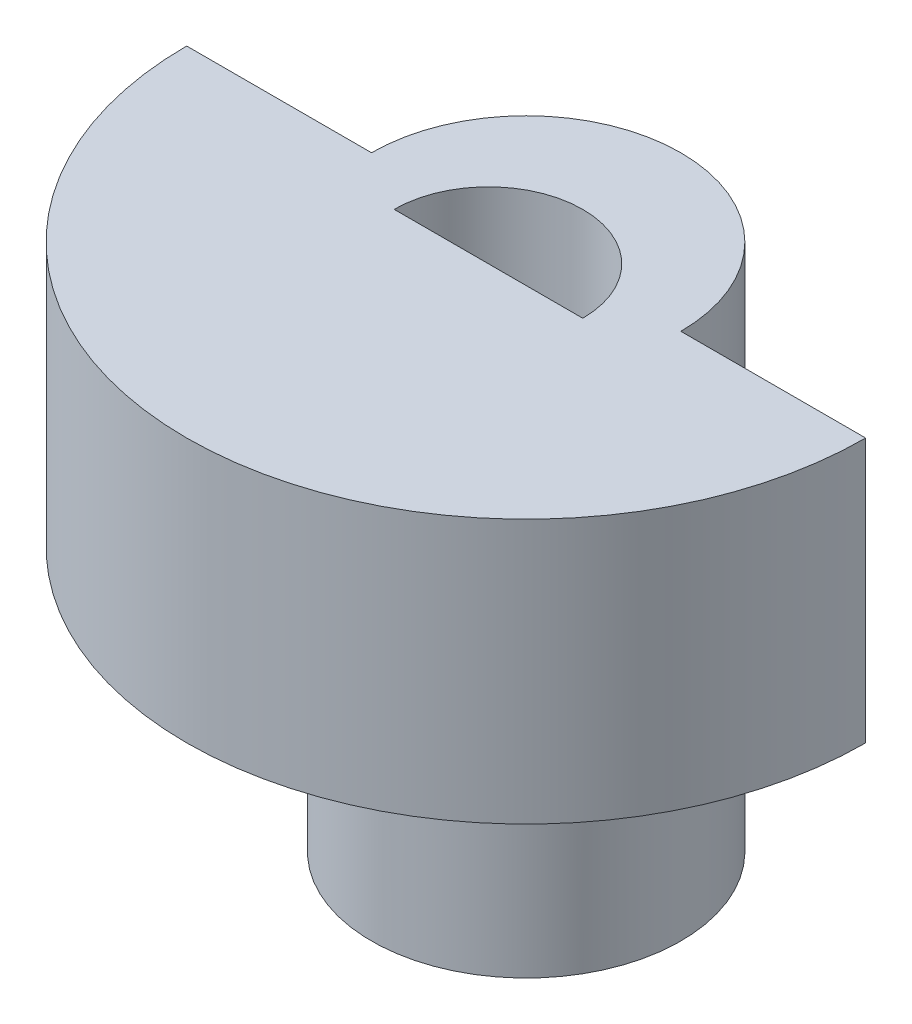
SolidWorks part; units mm, degrees
ref_plane "Front Plane" through (0, 0, 0) normal (0, 0, 1) x (1, 0, 0)
ref_plane "Top Plane" through (0, 0, 0) normal (0, 1, 0) x (1, 0, 0)
ref_plane "Right Plane" through (0, 0, 0) normal (1, 0, 0) x (0, 0, -1)
sketch "Sketch1" plane through (0, 0, 0) normal (0, 1, 0) x (1, 0, 0)
  line L0 (4.1, 0) -> (9, 0)
  line L1 (-4.1, 0) -> (-9, 0)
  arc A0 (-9, 0) -> (9, 0) centre (0, 0) ccw
  arc A1 (4.1, 0) -> (-4.1, 0) centre (0, 0) ccw
  dimension "D1" = 18
  dimension "D2" = 4.1
extrude "Boss-Extrude1" add sketch "Sketch1" along normal blind 7
sketch "Sketch2" plane through (0, 0, 0) normal (0, -1, 0) x (1, 0, 0)
  circle A0 centre (0, 0) radius 4.1
extrude "Boss-Extrude2" add sketch "Sketch2" along normal blind 7
sketch "Sketch3" plane through (0, 7, 0) normal (0, 1, 0) x (1, 0, 0)
  line L0 (2.5, -1) -> (-2.5, -1)
  line L1 (0, 0) -> (0, -1) construction
  arc A0 (2.5, -1) -> (-2.5, -1) centre (0, -1) ccw
  dimension "D2" = 1
  dimension "D3" = 2.5
  dimension "D1" = 5
extrude "Cut-Extrude1" cut sketch "Sketch3" against normal through all contours A0 L0
